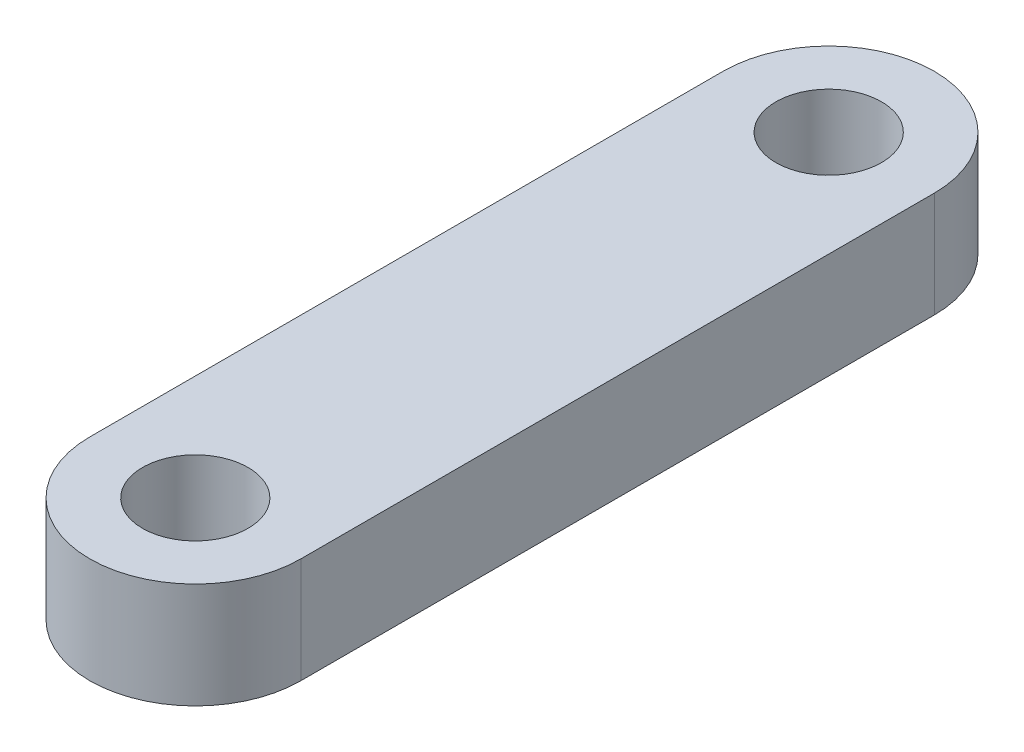
SolidWorks part; units mm, degrees
material "ABS"
ref_plane "Front Plane" through (0, 0, 0) normal (0, 0, 1) x (1, 0, 0)
ref_plane "Top Plane" through (0, 0, 0) normal (0, 1, 0) x (1, 0, 0)
ref_plane "Right Plane" through (0, 0, 0) normal (1, 0, 0) x (0, 0, -1)
sketch "Sketch1" plane through (0, 0, 0) normal (0, 1, 0) x (1, 0, 0)
  line L0 (0, 0) -> (0, -76.2)
  line L1 (25.4, 0) -> (25.4, -76.2)
  arc A0 (0, 0) -> (25.4, 0) centre (12.7, 0) cw
  arc A1 (0, -76.2) -> (25.4, -76.2) centre (12.7, -76.2) ccw
  circle A2 centre (12.7, 0) radius 6.35
  circle A3 centre (12.7, -76.2) radius 6.35
  dimension "D3" = 12.7
  dimension "D1" = 76.2
  dimension "D2" = 25.4
extrude "Boss-Extrude1" add sketch "Sketch1" along normal blind 12.7
